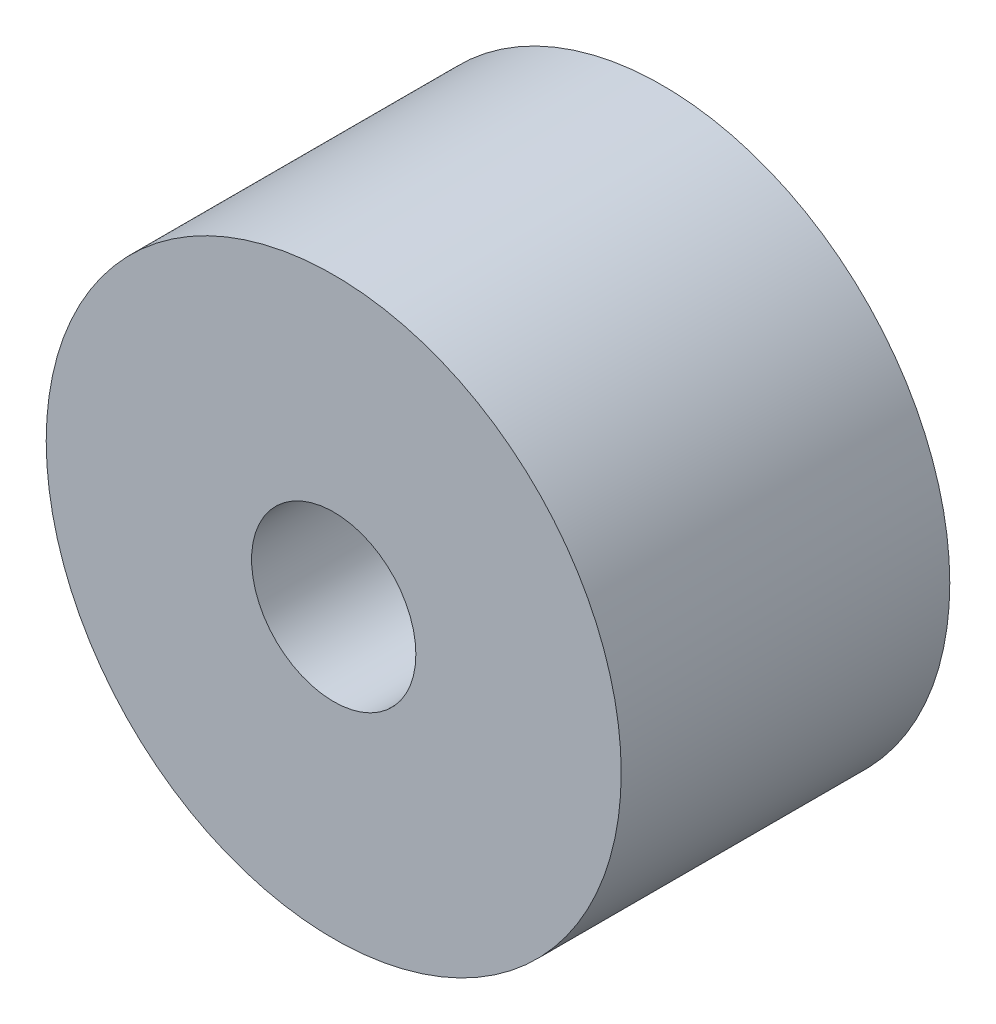
SolidWorks part; units mm, degrees
ref_plane "Alzado" through (0, 0, 0) normal (0, 0, 1) x (1, 0, 0)
ref_plane "Planta" through (0, 0, 0) normal (0, 1, 0) x (1, 0, 0)
ref_plane "Vista lateral" through (0, 0, 0) normal (1, 0, 0) x (0, 0, -1)
sketch "Croquis1" plane through (0, 0, 0) normal (0, 0, 1) x (1, 0, 0)
  circle A0 centre (0, 0) radius 17.5
  circle A1 centre (0, 0) radius 5
  dimension "D1" = 35
  dimension "D2" = 10
extrude "Saliente-Extruir1" add sketch "Croquis1" along normal mid plane 20
